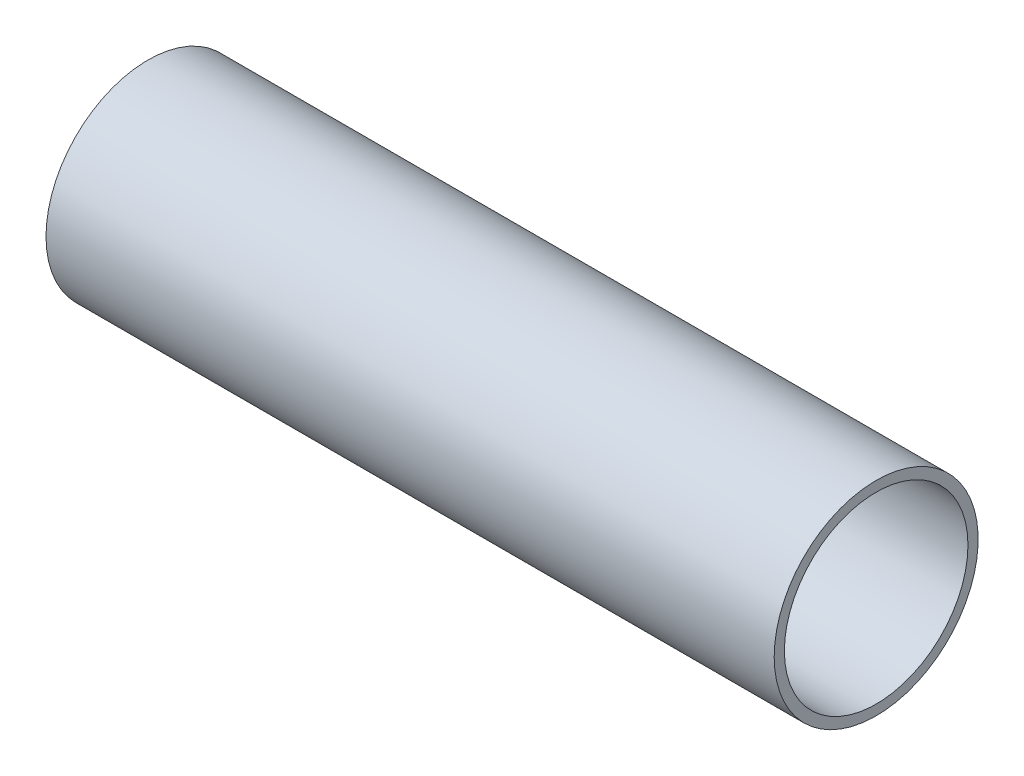
SolidWorks part; units mm, degrees
material "6061 Alloy"
ref_plane "Front Plane" through (0, 0, 0) normal (0, 0, 1) x (1, 0, 0)
ref_plane "Top Plane" through (0, 0, 0) normal (0, 1, 0) x (1, 0, 0)
ref_plane "Right Plane" through (0, 0, 0) normal (1, 0, 0) x (0, 0, -1)
sketch "Sketch1" plane through (0, 0, 0) normal (0, 1, 0) x (1, 0, 0)
  line L0 (-135.4711, 0) -> (171.1561, 0) construction
  line L1 (-56.6738, 14.2875) -> (56.6738, 14.2875)
  line L2 (-56.6738, 14.2875) -> (-56.6738, 15.875)
  line L3 (-56.6738, 15.875) -> (56.6738, 15.875)
  line L4 (56.6738, 15.875) -> (56.6738, 14.2875)
  point P5 (0, 14.2875)
  dimension "D1" = 113.3475
  dimension "D2" = 1.5875
  dimension "D3" = 15.875
revolve "Revolve1" add sketch "Sketch1" angle 360 about L0
